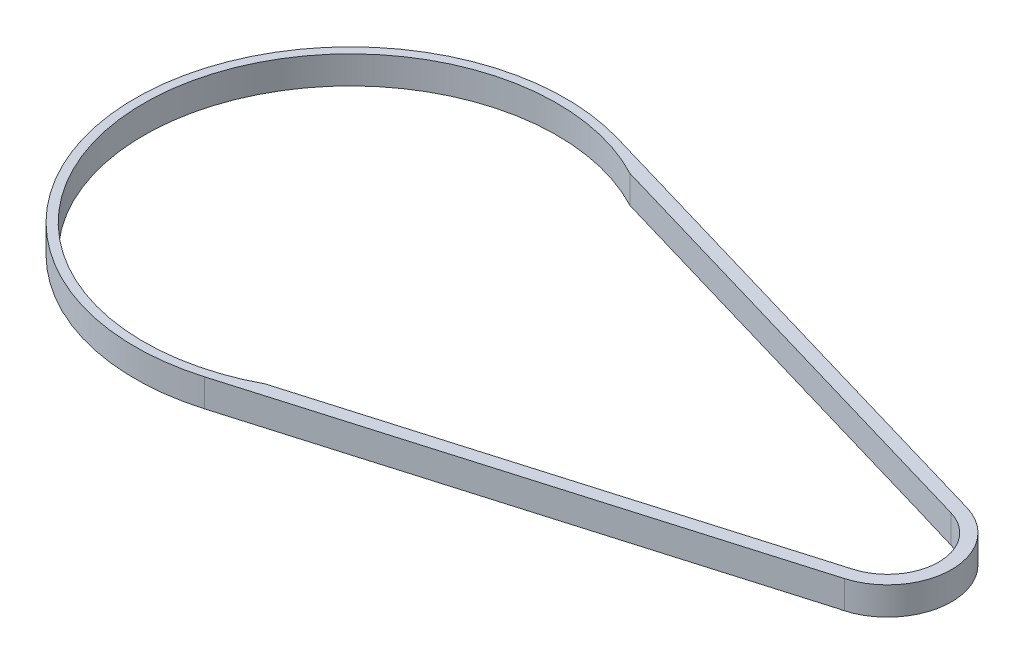
SolidWorks part; units mm, degrees
ref_plane "Front Plane" through (0, 0, 0) normal (0, 0, 1) x (1, 0, 0)
ref_plane "Top Plane" through (0, 0, 0) normal (0, 1, 0) x (1, 0, 0)
ref_plane "Right Plane" through (0, 0, 0) normal (1, 0, 0) x (0, 0, -1)
sketch "Sketch1" plane through (0, 13.4336, 0) normal (0, -1, 0) x (-1, 0, 0)
  circle A0 centre (-83.7764, 38.8853) radius 48.006
  circle A1 centre (-83.7764, 38.8853) radius 50.006
  dimension "D1" = 96.0121
  dimension "D2" = 2
extrude "Boss-Extrude1" add sketch "Sketch1" along normal blind 6.45
sketch "Sketch2" plane through (0, 17.9836, 0) normal (0, -1, 0) x (-1, 0, 0)
  circle A0 centre (-208.586, 38.8853) radius 11.85
  circle A1 centre (-208.586, 38.8853) radius 11.85 construction
extrude "Extrude-Thin1" add sketch "Sketch2" along normal blind 6.5 from offset 4.55 separate body thin
sketch "Sketch3" plane through (0, 6.9836, 0) normal (0, -1, 0) x (-1, 0, 0)
  line L0 (-208.586, 38.8853) -> (-154.6149, 38.8853) construction
  line L1 (-97.862, 86.8666) -> (-212.7689, 53.134)
  line L2 (-113.386, 79.1827) -> (-203.3364, 52.7765)
  line L5 (-113.386, -1.412) -> (-203.3364, 24.9942)
  line L6 (-97.862, -9.0959) -> (-212.7689, 24.6366)
  circle A1 centre (-208.586, 38.8853) radius 14.85 construction
  circle A2 centre (-83.7764, 38.8853) radius 50.006 construction
  arc A3 (-97.862, 86.8666) -> (-113.386, 79.1827) centre (-83.7764, 38.8853) ccw
  arc A4 (-203.3364, 52.7765) -> (-212.7689, 53.134) centre (-208.586, 38.8853) ccw
  arc A5 (-203.3364, 24.9942) -> (-212.7689, 24.6366) centre (-208.586, 38.8853) cw
  arc A6 (-97.862, -9.0959) -> (-113.386, -1.412) centre (-83.7764, 38.8853) cw
  dimension "D1" = 3
extrude "Boss-Extrude2" add sketch "Sketch3" against normal up to surface (6.45 mm away)
sketch "Sketch4" plane through (0, 6.9836, 0) normal (0, -1, 0) x (-1, 0, 0)
  line L0 (-113.386, 79.1827) -> (-106.3697, 81.2424)
  line L1 (-203.3364, 52.7765) -> (-113.386, 79.1827) construction
  line L3 (-113.386, -1.412) -> (-106.3697, -3.4718)
  line L4 (-113.386, -1.412) -> (-203.3364, 24.9942) construction
  arc A0 (-113.386, -1.412) -> (-113.386, 79.1827) centre (-83.7764, 38.8853) cw
  circle A1 centre (-83.7764, 38.8853) radius 48.006 construction
  arc A2 (-106.3697, -3.4718) -> (-106.3697, 81.2424) centre (-83.7764, 38.8853) cw
extrude "Cut-Extrude1" cut sketch "Sketch4" against normal through all
sketch "Sketch5" plane through (0, 6.9336, 0) normal (0, -1, 0) x (-1, 0, 0)
  line L0 (-203.3364, 24.9942) -> (-204.7707, 25.4152)
  line L1 (-106.3697, -3.4718) -> (-203.3364, 24.9942) construction
  line L2 (-203.3364, 52.7765) -> (-204.7707, 52.3554)
  line L3 (-204.7707, 25.4152) -> (-204.7707, 52.3554)
  arc A0 (-203.3364, 52.7765) -> (-203.3364, 24.9942) centre (-208.586, 38.8853) cw
  circle A1 centre (-208.586, 38.8853) radius 14.85 construction
  circle A2 centre (-208.586, 38.8853) radius 14 construction
  circle A4 centre (-208.586, 38.8853) radius 14 construction
extrude "Cut-Extrude2" cut sketch "Sketch5" against normal through all
sketch "Sketch6" plane through (0, 13.4336, 0) normal (0, 1, 0) x (1, 0, 0)
  line L0 (204.7707, 25.4152) -> (211.9238, 27.5151)
  line L1 (106.3697, -3.4718) -> (204.7707, 25.4152) construction
  line L2 (204.7707, 27.6663) -> (204.7707, 25.4152)
  line L3 (208.586, 38.8853) -> (197.4883, 38.8853) construction
  line L4 (204.7707, 50.1043) -> (204.7707, 52.3554)
  line L5 (204.7707, 52.3554) -> (211.9238, 50.2555)
  arc A0 (204.7707, 27.6663) -> (204.7707, 50.1043) centre (208.586, 38.8853) ccw construction
  arc A1 (211.9238, 27.5151) -> (204.7707, 27.6663) centre (208.586, 38.8853) cw
  arc A2 (211.9238, 50.2555) -> (204.7707, 50.1043) centre (208.586, 38.8853) ccw
extrude "Cut-Extrude3" cut sketch "Sketch6" against normal through all both and the other way through all
